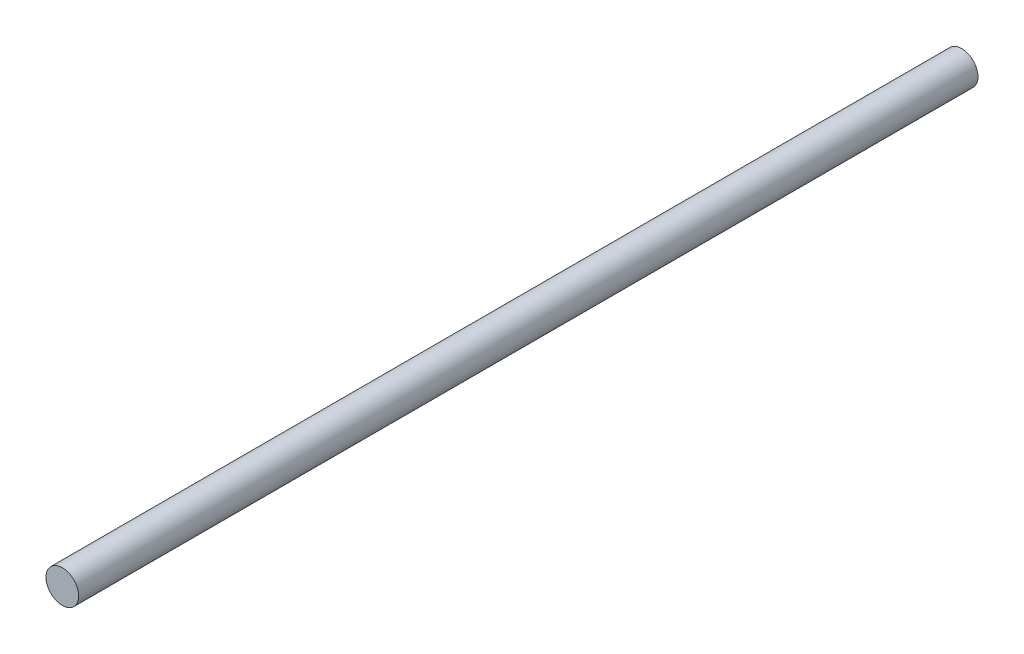
SolidWorks part; units mm, degrees
ref_plane "Front" through (0, 0, 0) normal (0, 0, 1) x (1, 0, 0)
ref_plane "Top" through (0, 0, 0) normal (0, 1, 0) x (1, 0, 0)
ref_plane "Right" through (0, 0, 0) normal (1, 0, 0) x (0, 0, -1)
sketch "Sketch1" plane through (0, 0, 0) normal (0, 0, 1) x (1, 0, 0)
  circle A0 centre (0, 0) radius 0.8
  dimension "D1" = 1.6
extrude "Boss-Extrude1" add sketch "Sketch1" along normal blind 44
